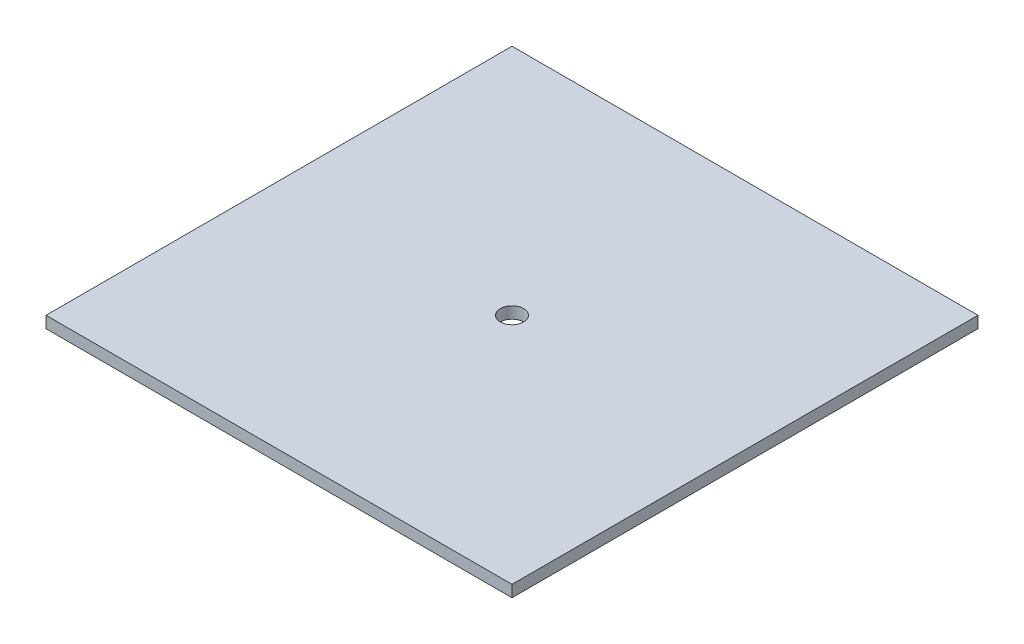
SolidWorks part; units mm, degrees
ref_plane "Front Plane" through (0, 0, 0) normal (0, 0, 1) x (1, 0, 0)
ref_plane "Top Plane" through (0, 0, 0) normal (0, 1, 0) x (1, 0, 0)
ref_plane "Right Plane" through (0, 0, 0) normal (1, 0, 0) x (0, 0, -1)
sketch "Sketch1" plane through (0, 0, 0) normal (0, 1, 0) x (1, 0, 0)
  line L1 (-127, 127) -> (127, 127)
  line L2 (-127, 127) -> (-127, -127)
  line L3 (-127, -127) -> (127, -127)
  line L4 (127, 127) -> (127, -127)
  line L5 (-127, 127) -> (127, -127) construction
  line L6 (-127, -127) -> (127, 127) construction
  circle A0 centre (0, 0) radius 6.35
  point P0 (0, 0)
  dimension "D3" = 12.7
  dimension "D1" = 254
  dimension "D2" = 254
extrude "Boss-Extrude1" add sketch "Sketch1" along normal blind 6.35
